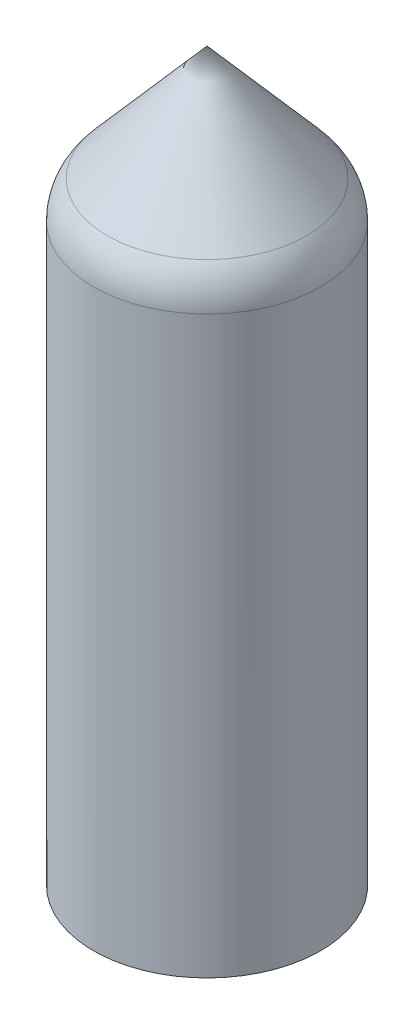
SolidWorks part; units mm, degrees
ref_plane "Alzado" through (0, 0, 0) normal (0, 0, 1) x (1, 0, 0)
ref_plane "Planta" through (0, 0, 0) normal (0, 1, 0) x (1, 0, 0)
ref_plane "Vista lateral" through (0, 0, 0) normal (1, 0, 0) x (0, 0, -1)
sketch "Croquis1" plane through (0, 0, 0) normal (0, 0, 1) x (1, 0, 0)
  line L0 (0, 0) -> (0, -5) construction
  line L1 (0, 0) -> (-20, 0) construction
  line L2 (0, -5) -> (-20, -5) construction
  line L3 (-20, 0) -> (-20, -5) construction
  line L4 (-20, 0) -> (-17, 0) construction
  line L5 (-20, 0) -> (-20, 100) construction
  line L6 (-17, 0) -> (-17, 100) construction
  line L7 (-17, 100) -> (0, 100) construction
  line L8 (0, 0) -> (0, 100) construction
  line L9 (0, 100) -> (0, 120) construction
  line L15 (-20, -5) -> (-20, 100)
  line L19 (-17, 100) -> (-17, 0)
  line L21 (0, 120) -> (0, 123) construction
  line L22 (-17, 100) -> (0, 120)
  line L23 (0, 120) -> (0, 123)
  line L24 (0, 123) -> (-20, 100)
  line L25 (-20, -5) -> (-10, -5)
  line L26 (-10, -5) -> (-10, 0)
  line L27 (-10, 0) -> (-17, 0)
  dimension "D1" = 5
  dimension "D2" = 20
  dimension "D3" = 3
  dimension "D4" = 100
  dimension "D5" = 20
  dimension "D6" = 3
  dimension "D7" = 100
  dimension "D8" = 10
revolve "Revolución3" add sketch "Croquis1" angle 360 about L8
fillet "Redondeo1" radius 10 1 edges at (0, 100, -20)
sketch "Croquis4" plane through (0, -5, 0) normal (0, -1, 0) x (1, 0, 0)
  line L0 (20, 0) -> (-20, 0) construction
  line L1 (0, -20) -> (0, 20) construction
  line L2 (20, 0) -> (10, 0) construction
  line L3 (20, 0) -> (12.5, 0) construction
  circle A0 centre (0, 0) radius 20 construction
  circle A1 centre (0, 0) radius 10 construction
  circle A2 centre (12.5, 0) radius 1.65
  circle A3 centre (-12.5, 0) radius 1.65
  dimension "D2" = 3.3
  dimension "D1" = 7.5
extrude "Cortar-Extruir1" cut sketch "Croquis4" against normal blind 5
sketch "Croquis5" plane through (0, 0, 0) normal (0, 1, 0) x (1, 0, 0)
  line L1 (-12.5, 3.4) -> (-15.4445, 1.7)
  line L2 (-15.4445, 1.7) -> (-15.4445, -1.7)
  line L3 (-15.4445, -1.7) -> (-12.5, -3.4)
  line L4 (-12.5, -3.4) -> (-9.5555, -1.7)
  line L5 (-9.5555, -1.7) -> (-9.5555, 1.7)
  line L6 (-9.5555, 1.7) -> (-12.5, 3.4)
  line L7 (12.5, 3.4) -> (9.5555, 1.7)
  line L8 (9.5555, 1.7) -> (9.5555, -1.7)
  line L9 (9.5555, -1.7) -> (12.5, -3.4)
  line L10 (12.5, -3.4) -> (15.4445, -1.7)
  line L11 (15.4445, -1.7) -> (15.4445, 1.7)
  line L12 (15.4445, 1.7) -> (12.5, 3.4)
  circle A0 centre (-12.5, 0) radius 2.9445 construction
  circle A1 centre (12.5, 0) radius 2.9445 construction
  dimension "D1" = 3.4
  dimension "D2" = 3.4
extrude "Cortar-Extruir2" cut sketch "Croquis5" against normal blind 2
